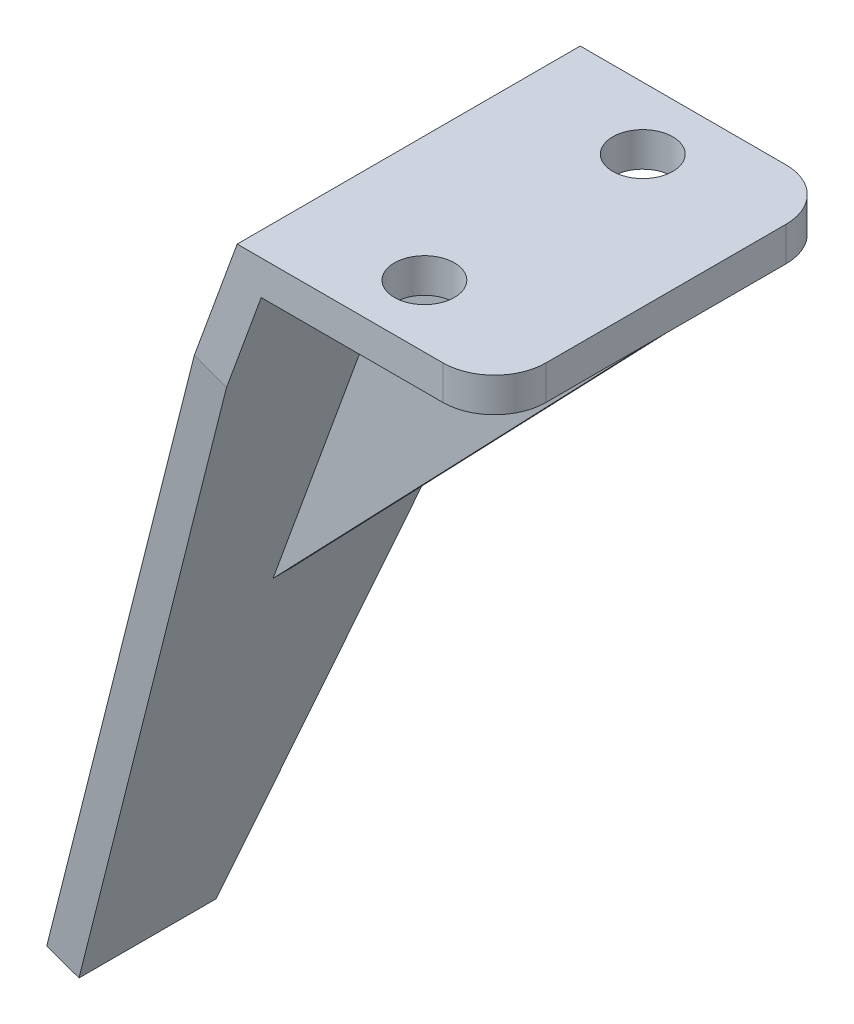
SolidWorks part; units mm, degrees
ref_plane "Front Plane" through (0, 0, 0) normal (0, 0, 1) x (1, 0, 0)
ref_plane "Top Plane" through (0, 0, 0) normal (0, 1, 0) x (1, 0, 0)
ref_plane "Right Plane" through (0, 0, 0) normal (1, 0, 0) x (0, 0, -1)
sketch "Sketch1" plane through (0, 0, 0) normal (0, 0, 1) x (1, 0, 0)
  line L0 (-7.5027, -23.4958) -> (-9.3821, -22.8118)
  line L1 (-7.5027, -23.4958) -> (9.1193, 22.1729)
  line L2 (-9.3821, -22.8118) -> (7.7189, 24.1729)
  line L4 (-7.5027, -23.4958) -> (7.7189, 24.1729) construction
  line L5 (-9.3821, -22.8118) -> (9.1193, 22.1729) construction
  line L6 (7.7189, 24.1729) -> (22.7189, 24.1729)
  line L7 (22.7189, 24.1729) -> (22.7189, 22.1729)
  line L8 (22.7189, 22.1729) -> (9.1193, 22.1729)
  point P0 (21.3984, 19.7955)
  point P1 (0, 0)
  point P7 (17.288, 21.012)
  point P10 (16.1694, 20.8334)
  point P11 (18.4161, 20.4009)
  dimension "D1" = 2
  dimension "D2" = 2
  dimension "D3" = 15
  dimension "D4" = 50
  dimension "D5" = 70
extrude "Boss-Extrude1" add sketch "Sketch1" along normal mid plane 20
sketch "Sketch2" plane through (0, 0, 0) normal (0, 0, 1) x (1, 0, 0)
  line L0 (22.7189, 22.1729) -> (0.8083, -0.6615)
  line L2 (-7.5027, -23.4958) -> (9.1193, 22.1729) construction
  line L3 (0.8083, -0.6615) -> (9.1193, 22.1729)
  line L4 (9.1193, 22.1729) -> (22.7189, 22.1729)
  line L5 (22.7189, 22.1729) -> (22.7189, 24.1729) construction
  line L6 (9.1193, 22.1729) -> (22.7189, 22.1729) construction
  point P2 (24.0088, 26.2152)
extrude "Boss-Extrude2" add sketch "Sketch2" along normal blind 1
chamfer "Chamfer1" distance 6 angle 82 2 edges at (-8.4424, -23.1538, -10) (-8.4424, -23.1538, 10)
sketch "Sketch3" plane through (0, 24.1729, 0) normal (0, 1, 0) x (1, 0, 0)
  line L0 (15, 6.365) -> (15, -6.365) construction
  line L1 (15, 0) -> (0, 0) construction
  circle A0 centre (15, 6.365) radius 1.75
  circle A1 centre (15, -6.365) radius 1.75
  dimension "D3" = 3.5
  dimension "D4" = 3.5
  dimension "D1" = 15
  dimension "D2" = 12.73
extrude "Cut-Extrude1" cut sketch "Sketch3" against normal through all
fillet "Fillet1" radius 3 2 edges at (22.7189, 23.1729, 10) (22.7189, 23.1729, -10)
